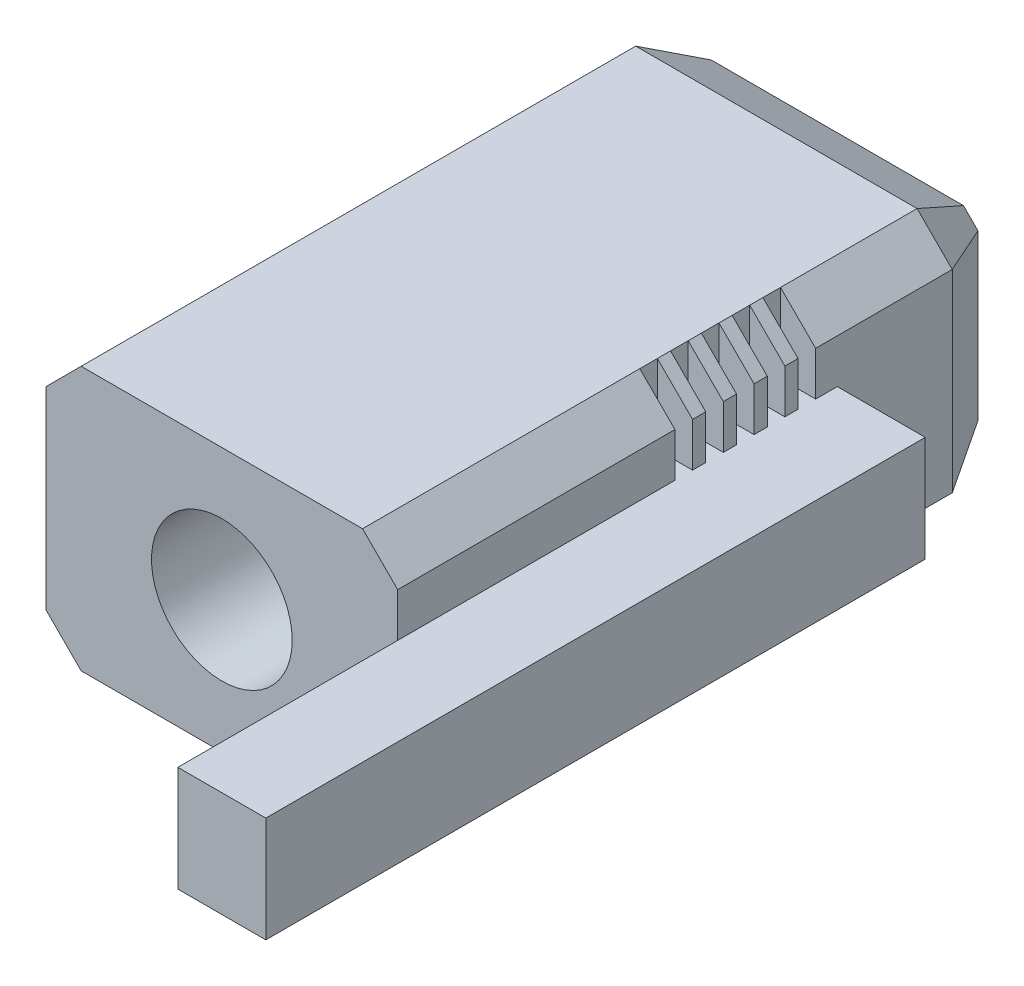
SolidWorks part; units mm, degrees
ref_plane "Front Plane" through (0, 0, 0) normal (0, 0, 1) x (1, 0, 0)
ref_plane "Top Plane" through (0, 0, 0) normal (0, 1, 0) x (1, 0, 0)
ref_plane "Right Plane" through (0, 0, 0) normal (1, 0, 0) x (0, 0, -1)
sketch "Sketch1" plane through (0, 0, 0) normal (0, 0, 1) x (1, 0, 0)
  line L0 (-10, 7.5) -> (-10, -7.5)
  line L1 (-10, 7.5) -> (10, 7.5)
  line L2 (-10, -7.5) -> (10, -7.5)
  line L3 (10, 7.5) -> (10, -7.5)
  line L4 (-10, 7.5) -> (10, -7.5) construction
  dimension "D1" = 20
  dimension "D2" = 15
extrude "Boss-Extrude1" add sketch "Sketch1" along normal blind 35
sketch "Sketch2" plane through (0, 0, 35) normal (0, 0, 1) x (1, 0, 0)
  circle A1 centre (0, 0) radius 4
  dimension "D3" = 8
extrude "Cut-Extrude1" cut sketch "Sketch2" against normal through all
chamfer "Chamfer1" distance 2 angle 45 4 edges at (-10, 7.5, 17.5) (-10, -7.5, 17.5) (10, -7.5, 17.5) (10, 7.5, 17.5)
chamfer "Chamfer2" distance 2 angle 60 8 edges at (10, 0, 0) (9, 6.5, 0) (0, 7.5, 0) (-9, 6.5, 0) (-10, 0, 0) (-9, -6.5, 0) (9, -6.5, 0) (0, -7.5, 0)
sketch "Sketch4" plane through (0, -7.5, 0) normal (0, -1, 0) x (1, 0, 0)
  line L0 (-8, 35) -> (-8, 3.4641) construction
  line L1 (-8, 11.2321) -> (-10, 11.2321)
  line L2 (-8, 11.2321) -> (-8, 12.2321)
  line L3 (-8, 12.2321) -> (-10, 12.2321)
  line L4 (-10, 11.2321) -> (-10, 12.2321)
  line L5 (-10, 3.4641) -> (-10, 35) construction
  line L6 (10, 19.2321) -> (-8, 19.2321) construction
  line L7 (-8, 12.9821) -> (-10, 12.9821)
  line L8 (-8, 12.9821) -> (-8, 13.9821)
  line L9 (-8, 13.9821) -> (-10, 13.9821)
  line L10 (-10, 12.9821) -> (-10, 13.9821)
  line L11 (-8, 14.7321) -> (-10, 14.7321)
  line L12 (-8, 14.7321) -> (-8, 15.7321)
  line L13 (-8, 15.7321) -> (-10, 15.7321)
  line L14 (-10, 14.7321) -> (-10, 15.7321)
  line L15 (-8, 16.4821) -> (-10, 16.4821)
  line L16 (-8, 16.4821) -> (-8, 17.4821)
  line L17 (-8, 17.4821) -> (-10, 17.4821)
  line L18 (-10, 16.4821) -> (-10, 17.4821)
  line L19 (-8, 18.2321) -> (-10, 18.2321)
  line L20 (-8, 18.2321) -> (-8, 19.2321)
  line L21 (-8, 19.2321) -> (-10, 19.2321)
  line L22 (-10, 18.2321) -> (-10, 19.2321)
  line L23 (10, 35) -> (10, 3.4641) construction
  line L24 (0, 0) -> (0, 19.2321) construction
  line L25 (10, 18.2321) -> (10, 19.2321)
  line L26 (8, 19.2321) -> (10, 19.2321)
  line L27 (8, 18.2321) -> (8, 19.2321)
  line L28 (8, 18.2321) -> (10, 18.2321)
  line L29 (10, 16.4821) -> (10, 17.4821)
  line L30 (8, 17.4821) -> (10, 17.4821)
  line L31 (8, 16.4821) -> (8, 17.4821)
  line L32 (8, 16.4821) -> (10, 16.4821)
  line L33 (10, 14.7321) -> (10, 15.7321)
  line L34 (8, 15.7321) -> (10, 15.7321)
  line L35 (8, 14.7321) -> (8, 15.7321)
  line L36 (8, 14.7321) -> (10, 14.7321)
  line L37 (10, 12.9821) -> (10, 13.9821)
  line L38 (8, 13.9821) -> (10, 13.9821)
  line L39 (8, 12.9821) -> (8, 13.9821)
  line L40 (8, 12.9821) -> (10, 12.9821)
  line L41 (10, 11.2321) -> (10, 12.2321)
  line L42 (8, 12.2321) -> (10, 12.2321)
  line L43 (8, 11.2321) -> (8, 12.2321)
  line L44 (8, 11.2321) -> (10, 11.2321)
  dimension "D2" = 1
  dimension "D4" = 0.75
  dimension "D3" = 5
extrude "Cut-Extrude2" cut sketch "Sketch4" against normal through all
sketch "Sketch5" plane through (0, -7.5, 0) normal (0, -1, 0) x (1, 0, 0)
  line L0 (-2, 14) -> (-2, 6)
  line L1 (-2, 14) -> (2, 14)
  line L2 (-2, 6) -> (2, 6)
  line L3 (2, 14) -> (2, 6)
  line L4 (0, 6) -> (0, 0) construction
  line L5 (0, 14) -> (0, 9) construction
  circle A0 centre (0, 9) radius 1.25
  dimension "D3" = 2.5
  dimension "D4" = 5
  dimension "D1" = 4
  dimension "D2" = 8
  dimension "D5" = 6
extrude "Cut-Extrude3" cut sketch "Sketch5" against normal blind 1
sketch "Sketch3" plane through (10, 0, 0) normal (1, 0, 0) x (0, 0, -1)
  line L0 (-47.5, 3) -> (-47.5, -3)
  line L1 (-47.5, 3) -> (-10, 3)
  line L2 (-47.5, -3) -> (-10, -3)
  line L3 (-10, 3) -> (-10, -3)
  line L4 (-35, 0) -> (-35, -3) construction
  line L5 (-35, 0) -> (-35, 3) construction
  line L8 (-35, -5.5) -> (-35, 5.5) construction
  dimension "D1" = 6
  dimension "D2" = 12.5
  dimension "D3" = 25
extrude "Boss-Extrude2" add sketch "Sketch3" along normal blind 5
sketch "Sketch6" plane through (10, 0, 0) normal (-1, 0, 0) x (0, 0, 1)
  line L0 (11.2321, 3) -> (19.2321, 3)
  line L1 (11.2321, 3) -> (11.2321, -3)
  line L2 (19.2321, 3) -> (19.2321, -3)
  line L3 (11.2321, -3) -> (19.2321, -3)
  line L4 (11.2321, 5.5) -> (11.2321, 3) construction
extrude "Boss-Extrude3" add sketch "Sketch6" along normal up to next
